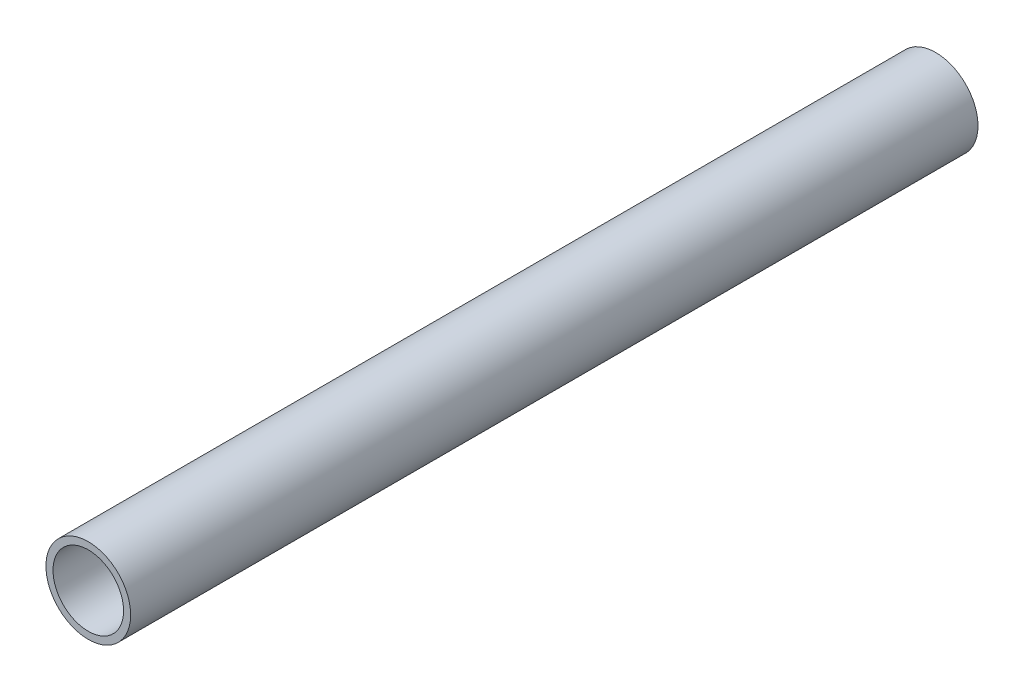
SolidWorks part; units mm, degrees
material "Thornel Mat VMA"
ref_plane "Front Plane" through (0, 0, 0) normal (0, 0, 1) x (1, 0, 0)
ref_plane "Top Plane" through (0, 0, 0) normal (0, 1, 0) x (1, 0, 0)
ref_plane "Right Plane" through (0, 0, 0) normal (1, 0, 0) x (0, 0, -1)
sketch "Sketch1" plane through (0, 0, 0) normal (0, 0, 1) x (1, 0, 0)
  circle A0 centre (0, 0) radius 3
  circle A1 centre (0, 0) radius 2.5
  dimension "D1" = 5
  dimension "D2" = 6
extrude "Boss-Extrude1" add sketch "Sketch1" along normal blind 60
